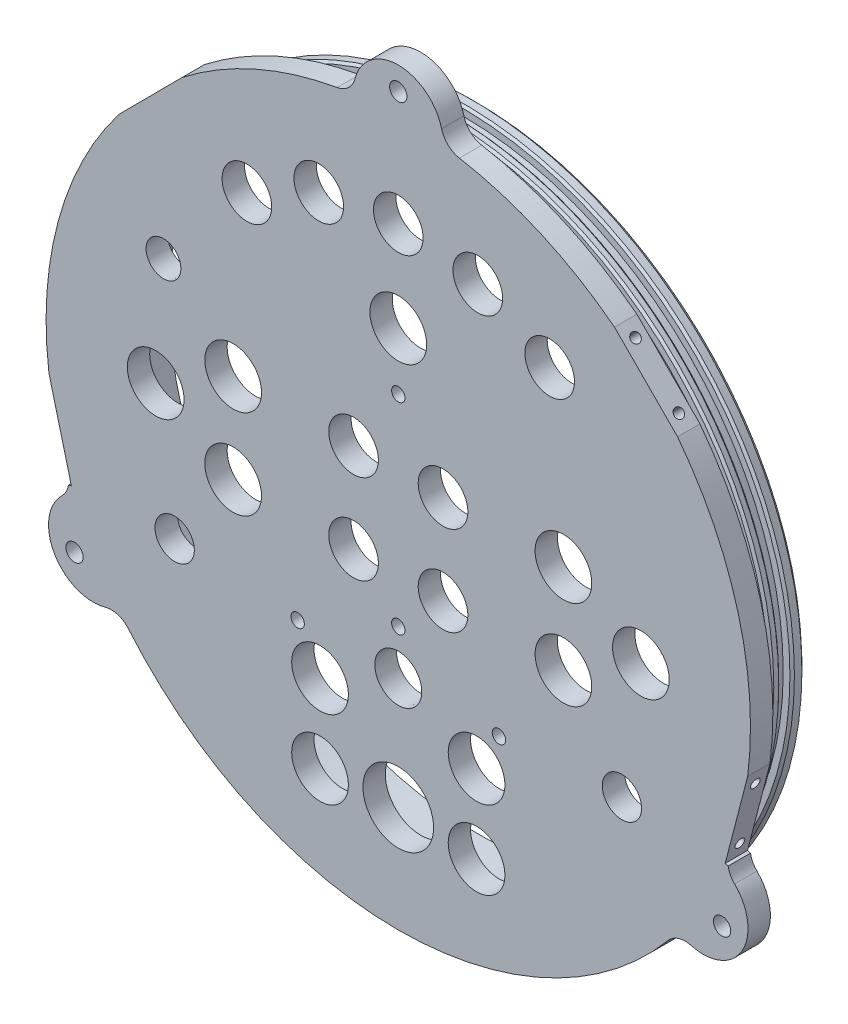
SolidWorks part; units mm, degrees
material "6061 Alloy"
ref_plane "Front Plane" through (0, 0, 0) normal (0, 0, 1) x (1, 0, 0)
ref_plane "Top Plane" through (0, 0, 0) normal (0, 1, 0) x (1, 0, 0)
ref_plane "Right Plane" through (0, 0, 0) normal (1, 0, 0) x (0, 0, -1)
sketch "Sketch1" plane through (0, 0, 0) normal (0, 0, 1) x (1, 0, 0)
  circle A0 centre (0, 0) radius 100.0125
extrude "Extrude1" add sketch "Sketch1" along normal blind 6.35
sketch "Sketch2" plane through (0, 0, 0) normal (0, 0, -1) x (-1, 0, 0)
  circle A0 centre (0, 0) radius 93.6625
extrude "Extrude2" add sketch "Sketch2" along normal blind 15.875
sketch "Sketch3" plane through (0, 0, -15.875) normal (0, 0, -1) x (-1, 0, 0)
  circle A0 centre (0, 0) radius 87.3125
extrude "Cut-Extrude1" cut sketch "Sketch3" against normal blind 15.875
sketch "Sketch4" plane through (0, 0, 0) normal (1, 0, 0) x (0, 0, -1)
  line L0 (15.875, 93.6625) -> (0, 93.6625) construction
  line L1 (2.8084, 93.6625) -> (5.9834, 93.6625)
  line L2 (2.8084, 93.6625) -> (2.8084, 91.1225)
  line L3 (2.8084, 91.1225) -> (5.9834, 91.1225)
  line L4 (5.9834, 93.6625) -> (5.9834, 91.1225)
  line L5 (0, 0) -> (42.3826, 0) construction
  line L6 (8.6645, 93.6625) -> (11.8395, 93.6625)
  line L7 (8.6645, 93.6625) -> (8.6645, 91.1225)
  line L8 (8.6645, 91.1225) -> (11.8395, 91.1225)
  line L9 (11.8395, 93.6625) -> (11.8395, 91.1225)
  dimension "D1" = 2.54
  dimension "D2" = 3.175
revolve "Cut-Revolve1" cut sketch "Sketch4" angle 360 about L5
chamfer "Chamfer1" distance 1.27 angle 45 1 edges at (-93.6625, 0, -15.875)
sketch "Sketch5" plane through (0, 0, 6.35) normal (0, 0, 1) x (1, 0, 0)
  circle A16 centre (0, 47.9573) radius 8.05
  circle A17 centre (0, 73.66) radius 7.05
  circle A18 centre (-63.5, -35.56) radius 5.588
  circle A19 centre (63.5, -35.56) radius 5.588
  dimension "D1" = 63.5
  dimension "D5" = 35.56
  dimension "D2" = 63.5
  dimension "D4" = 73.66
  dimension "D6" = 35.56
sketch "Sketch7" plane through (0, 0, 6.35) normal (0, 0, 1) x (1, 0, 0)
  line L0 (0, 0) -> (0, 100.0125) construction
  circle A0 centre (0, 0) radius 100.0125 construction
sketch "Sketch8" plane through (0, 0, 6.35) normal (0, 0, 1) x (1, 0, 0)
  line L0 (0, 0) -> (86.6134, -50.0063) construction
  line L1 (0, 0) -> (-86.6134, -50.0063) construction
  line L2 (0, 0) -> (0, 100.0125) construction
  circle A0 centre (0, 0) radius 100.0125 construction
  arc A1 (-12.6744, 99.2062) -> (12.6744, 99.2062) centre (0, 100.0125) cw
  arc A2 (92.2522, -38.6267) -> (79.5779, -60.5794) centre (86.6134, -50.0063) cw
  arc A3 (-92.2522, -38.6267) -> (-79.5779, -60.5794) centre (-86.6134, -50.0063) ccw
  arc A4 (-12.6744, 99.2062) -> (12.6744, 99.2062) centre (0, 0) cw
  arc A5 (92.2522, -38.6267) -> (79.5779, -60.5794) centre (0, 0) cw
  arc A6 (-92.2522, -38.6267) -> (-79.5779, -60.5794) centre (0, 0) ccw
  dimension "D1" = 12.7
  dimension "D2" = 12.7
  dimension "D3" = 12.7
  dimension "D4" = 120
  dimension "D5" = 120
extrude "Extrude3" add sketch "Sketch8" against normal up to surface (6.35 mm away) up to face at (100.0125, 0, 0)
sketch "Sketch10" plane through (0, 0, 6.35) normal (0, 0, 1) x (1, 0, 0)
  line L0 (0, 0) -> (0, 123.4907) construction
  line L1 (0, 0) -> (137.3268, -79.2857) construction
  line L2 (0, 0) -> (-146.5837, -84.6301) construction
extrude "Cut-Extrude2" cut sketch "Sketch5" against normal through all
hole_wizard "#10 (0.1935) Diameter Hole1" positions "3DSketch2" profile "Sketch11" hole size "#10" standard "Ansi Inch"
sketch3d "3DSketch2"
  line L0 (0, 0, 6.35) -> (0, 123.4907, 6.35) construction
  line L1 (0, 0, 6.35) -> (137.3268, -79.2857, 6.35) construction
  line L2 (0, 0, 6.35) -> (-146.5837, -84.6301, 6.35) construction
  point P0 (0, 106.1728, 6.35)
  point P4 (91.9483, -53.0864, 6.35)
  point P8 (-91.9483, -53.0864, 6.35)
  dimension "D1" = 106.3625
  dimension "D2" = 106.3625
  dimension "D3" = 106.3625
sketch "Sketch11" plane through (0, 106.1728, 6.35) normal (1, 0, 0) x (0, -1, 0)
  line L0 (0, 0) -> (0, 331.6766)
  line L1 (0, 331.6766) -> (2.4574, 330.2)
  line L2 (2.4574, 330.2) -> (2.4574, 0)
  line L5 (2.4574, 0) -> (0, 0)
  line L10 (0, 331.6766) -> (-2.4575, 330.2) construction
  line L11 (0, -6.35) -> (0, 107.95) construction
  dimension "Hole Dia." = 4.9149
  dimension "Hole Depth" = 330.2
  dimension "Drill Angle" = 118
chamfer "Chamfer2" distance 0.635 angle 45 4 edges at (93.6625, 0, -2.8084) (93.6625, 0, -5.9834) (93.6625, 0, -8.6645) (93.6625, 0, -11.8395)
sketch "Sketch15" plane through (0, 0, 6.35) normal (0, 0, 1) x (1, 0, 0)
  circle A0 centre (0, -69.85) radius 10.033
  dimension "D1" = 69.85
extrude "Cut-Extrude3" cut sketch "Sketch15" against normal through all
sketch "Sketch17" plane through (0, 0, 6.35) normal (0, 0, 1) x (1, 0, 0)
  line L0 (0, 106.1728) -> (0, 0) construction
  line L1 (-46.896, 12.7) -> (-46.896, -12.7) construction
  line L2 (-46.896, 0) -> (-107.9684, 0) construction
  line L3 (46.896, 0) -> (107.9684, 0) construction
  line L4 (46.896, 12.7) -> (46.896, -12.7) construction
  line L5 (0, 0) -> (-129.2921, 0) construction
  line L6 (68.8931, 0) -> (46.896, 12.7) construction
  line L7 (42.9911, 59.8127) -> (22.5831, 70.1128) construction
  line L8 (22.5831, 70.1128) -> (0, 73.66) construction
  line L9 (22.5831, 70.1128) -> (30.6624, 95.1962) construction
  line L10 (30.6624, 95.1962) -> (60.9252, 85.4486) construction
  line L11 (42.9911, 59.8127) -> (58.3716, 81.2112) construction
  line L12 (58.3716, 81.2112) -> (94.3714, 55.3359) construction
  line L13 (0, 0) -> (22.5831, 70.1128) construction
  line L14 (22.5831, 70.1128) -> (0, 73.66) construction
  line L15 (0, 73.66) -> (0, 0) construction
  line L16 (12.7, -12.7) -> (12.7, 0) construction
  line L17 (12.7, 12.7) -> (0, 12.7) construction
  line L19 (12.7, 0) -> (12.7, 12.7) construction
  circle A0 centre (-22.5831, 70.1128) radius 7.05
  circle A1 centre (-42.9911, 59.8127) radius 7.05
  circle A2 centre (-68.8931, 0) radius 8.05
  circle A3 centre (-46.896, -12.7) radius 8.05
  circle A4 centre (-46.896, 12.7) radius 8.05
  circle A5 centre (-12.7, 12.7) radius 7.05
  circle A6 centre (-12.7, -12.7) radius 7.05
  circle A7 centre (12.7, -12.7) radius 7.05
  circle A8 centre (12.7, 12.7) radius 7.05
  circle A9 centre (46.896, 12.7) radius 8.05
  circle A10 centre (46.896, -12.7) radius 8.05
  circle A11 centre (68.8931, 0) radius 8.05
  circle A12 centre (42.9911, 59.8127) radius 7.05
  circle A13 centre (22.5831, 70.1128) radius 7.05
  circle A15 centre (0, 0) radius 100.0125 construction
  dimension "D1" = 25.4
  dimension "D2" = 25.4
  dimension "D3" = 25.4
  dimension "D4" = 22.86
extrude "Cut-Extrude4" cut sketch "Sketch17" against normal through all
hole_wizard "#6 Clearance Hole1" positions "3DSketch7" profile "Sketch18" hole size "#6" standard "Ansi Inch"
sketch3d "3DSketch7"
  line L0 (0, 0, 0) -> (55.3338, 0, 0) construction
  line L2 (0, 0, 0) -> (0, -54.9677, 0) construction
  point P17 (28.575, -38.1, 0)
  point P19 (-28.575, -38.1, 0)
  dimension "D1" = 57.15
  dimension "D3" = 38.1
  dimension "D2" = 28.575
sketch "Sketch18" plane through (28.575, -38.1, 0) normal (1, 0, 0) x (0, 1, 0)
  line L0 (0, 0) -> (0, 13.8408)
  line L1 (0, 13.8408) -> (1.8986, 12.7)
  line L2 (1.8986, 12.7) -> (1.8986, 0)
  line L5 (1.8986, 0) -> (0, 0)
  line L10 (0, 13.8408) -> (-1.8987, 12.7) construction
  line L11 (0, -6.35) -> (0, 107.95) construction
  dimension "Hole Dia." = 3.7973
  dimension "Hole Depth" = 12.7
  dimension "Drill Angle" = 118
hole_wizard "Tap Drill for #6 Tap1" positions "3DSketch8" profile "Sketch19" hole size "#6-32" standard "Ansi Inch"
sketch3d "3DSketch8"
  line L0 (0, 0, 0) -> (-45.7945, 0, 0) construction
  line L2 (0, 0, 0) -> (0, 34.2452, 0) construction
  point P0 (34.925, 29.21, 0)
  point P2 (-34.925, 29.21, 0)
  point P4 (-25.4, 29.21, 0)
  point P6 (25.4, 29.21, 0)
  point P15 (44.45, -52.705, 0)
  point P17 (-44.45, -52.705, 0)
  dimension "D1" = 9.525
  dimension "D2" = 9.525
  dimension "D3" = 69.85
  dimension "D4" = 34.925
  dimension "D5" = 29.21
  dimension "D6" = 88.9
  dimension "D7" = 52.705
  dimension "D8" = 44.45
sketch "Sketch19" plane through (34.925, 29.21, 0) normal (1, 0, 0) x (0, 1, 0)
  line L0 (0, 0) -> (0, 4.1147)
  line L1 (0, 4.1147) -> (1.3525, 3.302)
  line L2 (1.3525, 3.302) -> (1.3525, 0)
  line L5 (1.3525, 0) -> (0, 0)
  line L10 (0, 4.1147) -> (-1.3526, 3.302) construction
  line L11 (0, -6.35) -> (0, 107.95) construction
  dimension "Hole Dia." = 2.7051
  dimension "Hole Depth" = 3.302
  dimension "Drill Angle" = 118
hole_wizard "1/4 NPT Tapped Hole1" positions "3DSketch9" profile "Sketch20" size "1/4" standard "Ansi Inch"
sketch3d "3DSketch9"
  line L0 (0, 0, 0) -> (0, -87.3125, 0) construction
  line L2 (0, 0, 0) -> (87.3125, 0, 0) construction
  circle A0 centre (0, 0, 0) radius 87.3125 construction
  point P9 (0, -38.1, 0)
  point P20 (0, 0, -87.3125)
  dimension "D2" = 38.1
sketch "Sketch20" plane through (0, -38.1, 0) normal (1, 0, 0) x (0, 1, 0)
  line L0 (0, 0) -> (0, 20.3603)
  line L1 (5.5626, 17.018) -> (0, 20.3603)
  line L2 (-5.5626, 17.018) -> (0, 20.3603) construction
  line L3 (5.5626, 17.018) -> (5.5626, 9.906)
  line L4 (5.5626, 9.906) -> (6.558, 9.906)
  line L5 (6.558, 9.906) -> (6.8546, 0)
  line L6 (-6.558, 9.906) -> (-6.8546, 0) construction
  line L7 (6.8546, 0) -> (0, 0)
  line L8 (0, -6.35) -> (0, 107.95) construction
  line L11 (-5.5626, 9.906) -> (-6.558, 9.906) construction
  dimension "Tap Drill Dia." = 11.1252
  dimension "Tap Drill Depth" = 17.018
  dimension "Thread Dia." = 13.7092
  dimension "Thread Angle" = 3.43
  dimension "Thread Depth" = 9.906
  dimension "Drill Angle" = 118
hole_wizard "1/8 NPT Tapped Hole1" positions "3DSketch6" profile "Sketch16" size "1/8" standard "Ansi Inch"
sketch3d "3DSketch6"
  line L0 (0, 0, 0) -> (87.3125, 0, 0) construction
  line L2 (0, 0, 0) -> (0, 87.3125, 0) construction
  circle A0 centre (0, 0, 0) radius 87.3125 construction
  point P3 (-66.675, 31.75, 0)
  point P10 (0, 0, -87.3125)
  dimension "D1" = 31.75
  dimension "D2" = 66.675
sketch "Sketch16" plane through (-66.675, 31.75, 0) normal (1, 0, 0) x (0, 1, 0)
  line L0 (0, 0) -> (0, 13.7095)
  line L1 (4.2164, 11.176) -> (0, 13.7095)
  line L2 (-4.2164, 11.176) -> (0, 13.7095) construction
  line L3 (4.2164, 11.176) -> (4.2164, 6.35)
  line L4 (4.2164, 6.35) -> (4.9362, 6.35)
  line L5 (4.9362, 6.35) -> (5.1263, 0)
  line L6 (-4.9362, 6.35) -> (-5.1263, 0) construction
  line L7 (5.1263, 0) -> (0, 0)
  line L8 (0, -6.35) -> (0, 107.95) construction
  line L11 (-4.2164, 6.35) -> (-4.9362, 6.35) construction
  dimension "Tap Drill Dia." = 8.4328
  dimension "Tap Drill Depth" = 11.176
  dimension "Thread Dia." = 10.2526
  dimension "Thread Angle" = 3.43
  dimension "Thread Depth" = 6.35
  dimension "Drill Angle" = 118
fillet "Fillet1" radius 6.35 6 edges at (92.2522, -38.6267, 3.175) (79.5779, -60.5794, 3.175) (-12.6744, 99.2062, 3.175) (12.6744, 99.2062, 3.175) (-79.5779, -60.5794, 3.175) (-92.2522, -38.6267, 3.175)
sketch "Sketch22" plane through (0, 0, 6.35) normal (0, 0, 1) x (1, 0, 0)
  line L0 (0, 0) -> (0, 100.0125) construction
  line L1 (-79.302, 60.94) -> (-70.3475, 69.946)
  line L2 (-70.9217, 70.5168) -> (0, 0) construction
  line L3 (0, 0) -> (-96.8054, -25.1239) construction
  line L4 (-70.3475, 69.946) -> (-61.393, 78.9519)
  line L5 (-99.2121, -12.6278) -> (-96.0218, -24.9205)
  line L6 (-96.0218, -24.9205) -> (-92.8314, -37.2133)
  line L7 (-79.302, 60.94) -> (-84.7318, 66.3388)
  line L8 (-66.8227, 84.3506) -> (-61.393, 78.9519)
  line L9 (-84.7318, 66.3388) -> (-66.8227, 84.3506)
  line L10 (-92.8314, -37.2133) -> (-99.2121, -38.8693)
  line L11 (-99.2121, -38.8693) -> (-105.5928, -14.2838)
  line L12 (-105.5928, -14.2838) -> (-99.2121, -12.6278)
  line L13 (105.5928, -14.2838) -> (99.2121, -12.6278)
  line L14 (99.2121, -38.8693) -> (105.5928, -14.2838)
  line L15 (92.8314, -37.2133) -> (99.2121, -38.8693)
  line L16 (84.7318, 66.3388) -> (66.8227, 84.3506)
  line L17 (66.8227, 84.3506) -> (61.393, 78.9519)
  line L18 (79.302, 60.94) -> (84.7318, 66.3388)
  line L19 (96.0218, -24.9205) -> (92.8314, -37.2133)
  line L20 (99.2121, -12.6278) -> (96.0218, -24.9205)
  line L21 (70.3475, 69.946) -> (61.393, 78.9519)
  line L22 (79.302, 60.94) -> (70.3475, 69.946)
  circle A0 centre (0, 0) radius 100.0125 construction
  dimension "D1" = 45.164
  dimension "D2" = 104.549
  dimension "D3" = 25.4
  dimension "D4" = 25.4
  dimension "D5" = 12.7
  dimension "D6" = 12.7
extrude "Cut-Extrude5" cut sketch "Sketch22" against normal through all
hole_wizard "Tap Drill for #6 Tap2" positions "3DSketch11" profile "Sketch23" hole size "#6-32" standard "Ansi Inch"
sketch3d "3DSketch11"
  line L0 (61.393, 78.9519, 3.175) -> (79.302, 60.94, 3.175) construction
  line L1 (61.393, 78.9519, 0) -> (61.393, 78.9519, 6.35) construction
  line L2 (79.302, 60.94, 0) -> (79.302, 60.94, 6.35) construction
  line L4 (99.2121, -12.6278, 3.175) -> (92.8314, -37.2133, 3.175) construction
  line L5 (99.2121, -12.6278, 0) -> (99.2121, -12.6278, 6.35) construction
  line L6 (92.8314, -37.2133, 0) -> (92.8314, -37.2133, 6.35) construction
  line L8 (-92.8314, -37.2133, 3.175) -> (-99.2121, -12.6278, 3.175) construction
  line L9 (-92.8314, -37.2133, 0) -> (-92.8314, -37.2133, 6.35) construction
  line L10 (-99.2121, -12.6278, 0) -> (-99.2121, -12.6278, 6.35) construction
  line L12 (-61.393, 78.9519, 3.175) -> (-79.302, 60.94, 3.175) construction
  line L13 (-61.393, 78.9519, 0) -> (-61.393, 78.9519, 6.35) construction
  line L14 (-79.302, 60.94, 0) -> (-79.302, 60.94, 6.35) construction
  line L16 (-96.0218, -24.9205, 6.35) -> (-96.0218, -24.9205, 0) construction
  line L17 (-92.8314, -37.2133, 6.35) -> (-99.2121, -12.6278, 6.35) construction
  line L18 (-92.8314, -37.2133, 0) -> (-99.2121, -12.6278, 0) construction
  line L20 (-70.3475, 69.946, 6.35) -> (-70.3475, 69.946, 0) construction
  line L21 (-79.302, 60.94, 6.35) -> (-61.393, 78.9519, 6.35) construction
  line L22 (-79.302, 60.94, 0) -> (-61.393, 78.9519, 0) construction
  line L24 (70.3475, 69.946, 6.35) -> (70.3475, 69.946, 0) construction
  line L25 (61.393, 78.9519, 6.35) -> (79.302, 60.94, 6.35) construction
  line L26 (61.393, 78.9519, 0) -> (79.302, 60.94, 0) construction
  line L28 (96.0218, -24.9205, 6.35) -> (96.0218, -24.9205, 0) construction
  line L29 (99.2121, -12.6278, 6.35) -> (92.8314, -37.2133, 6.35) construction
  line L30 (99.2121, -12.6278, 0) -> (92.8314, -37.2133, 0) construction
  point P0 (-93.8284, -33.3718, 3.175)
  point P2 (-98.2151, -16.4693, 3.175)
  point P4 (-76.5038, 63.7544, 3.175)
  point P6 (-64.1913, 76.1375, 3.175)
  point P8 (64.1913, 76.1375, 3.175)
  point P10 (76.5038, 63.7544, 3.175)
  point P12 (98.2151, -16.4693, 3.175)
  point P14 (93.8284, -33.3718, 3.175)
  dimension "D1" = 17.4625
  dimension "D2" = 8.7312
  dimension "D3" = 17.4625
  dimension "D4" = 8.7312
  dimension "D5" = 17.4625
  dimension "D6" = 8.7312
  dimension "D7" = 17.4625
  dimension "D8" = 8.7312
sketch "Sketch23" plane through (-93.8284, -33.3718, 3.175) normal (0, 0, 1) x (0.2512, -0.9679, 0)
  line L0 (0, 0) -> (0, 10.3377)
  line L1 (0, 10.3377) -> (1.3525, 9.525)
  line L2 (1.3525, 9.525) -> (1.3525, 0)
  line L5 (1.3525, 0) -> (0, 0)
  line L10 (0, 10.3377) -> (-1.3526, 9.525) construction
  line L11 (0, -6.35) -> (0, 107.95) construction
  dimension "Hole Dia." = 2.7051
  dimension "Hole Depth" = 9.525
  dimension "Drill Angle" = 118
hole_wizard "#6 Clearance Hole2" positions "Sketch25" profile "Sketch24" hole size "#6" standard "Ansi Inch"
sketch "Sketch25" plane through (0, 0, 6.35) normal (0, 0, 1) x (1, 0, 0)
  line L0 (0, 112.7125) -> (0, -100.0125) construction
  arc A0 (12.301, 103.1707) -> (-12.301, 103.1707) centre (0, 100.0125) ccw construction
  arc A1 (-76.6251, -64.2736) -> (76.6251, -64.2736) centre (0, 0) ccw construction
  point P0 (0, 31.75)
  point P1 (0, -25.4)
  dimension "D1" = 57.15
  dimension "D2" = 31.75
sketch "Sketch24" plane through (0, 31.75, 6.35) normal (1, 0, 0) x (0, -1, 0)
  line L0 (0, 0) -> (0, 7.4908)
  line L1 (0, 7.4908) -> (1.8986, 6.35)
  line L2 (1.8986, 6.35) -> (1.8986, 0)
  line L5 (1.8986, 0) -> (0, 0)
  line L10 (0, 7.4908) -> (-1.8986, 6.35) construction
  line L11 (0, -6.35) -> (0, 107.95) construction
  dimension "Hole Dia." = 3.7973
  dimension "Hole Depth" = 6.35
  dimension "Drill Angle" = 118
sketch "Sketch26" plane through (0, 0, 0) normal (0, 0, -1) x (-1, 0, 0)
  line L0 (0, 0) -> (0, -60.325) construction
  line L2 (22.225, -49.2125) -> (-22.225, -49.2125)
  line L3 (22.225, -49.2125) -> (22.225, -71.4375)
  line L4 (22.225, -71.4375) -> (-22.225, -71.4375)
  line L5 (-22.225, -49.2125) -> (-22.225, -71.4375)
  line L6 (22.225, -49.2125) -> (-22.225, -71.4375) construction
  line L7 (22.225, -71.4375) -> (-22.225, -49.2125) construction
  circle A0 centre (-22.225, -49.2125) radius 8.05
  circle A1 centre (-22.225, -71.4375) radius 8.05
  circle A2 centre (22.225, -49.2125) radius 8.05
  circle A3 centre (22.225, -71.4375) radius 8.05
  dimension "D1" = 16.1
  dimension "D5" = 16.1
  dimension "D6" = 16.1
  dimension "D7" = 16.1
  dimension "D2" = 60.325
  dimension "D3" = 44.45
  dimension "D4" = 22.225
extrude "Cut-Extrude6" cut sketch "Sketch26" against normal through all contours L2 A0 L5 | L5 A0 L2 | L3 A2 L2 | L2 A2 L3 | L4 A3 L3 | L3 A3 L4 | L5 A1 L4 | L4 A1 L5
